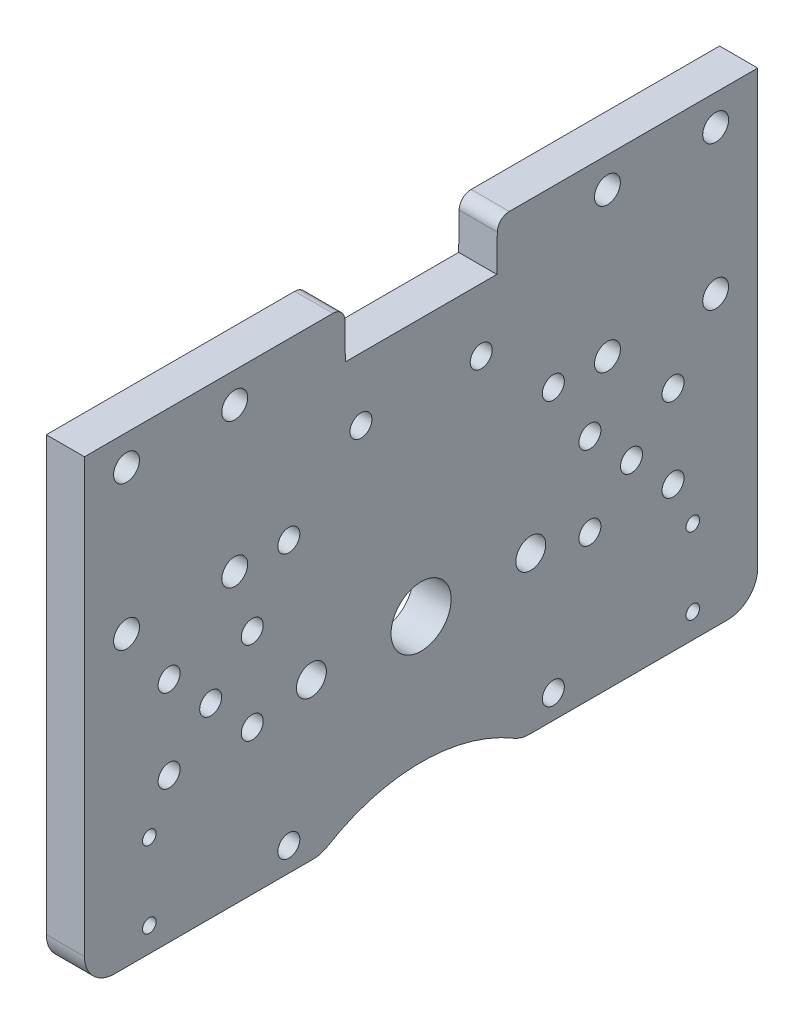
SolidWorks part; units mm, degrees
ref_plane "Front Plane" through (0, 0, 0) normal (0, 0, 1) x (1, 0, 0)
ref_plane "Top Plane" through (0, 0, 0) normal (0, 1, 0) x (1, 0, 0)
ref_plane "Right Plane" through (0, 0, 0) normal (1, 0, 0) x (0, 0, -1)
sketch "Sketch1" plane through (0, 0, 0) normal (1, 0, 0) x (0, 0, -1)
  line L1 (-56, -26) -> (56, -26)
  line L2 (-56, -26) -> (-56, 51)
  line L3 (-56, 51) -> (56, 51)
  line L4 (56, -26) -> (56, 51)
  point P0 (0, 0)
  point P6 (0, -26)
  dimension "D1" = 77
  dimension "D2" = 112
  dimension "D3" = 26
extrude "Boss-Extrude1" add sketch "Sketch1" along normal blind 6.35
sketch "Sketch2" plane through (6.35, 0, 0) normal (1, 0, 0) x (0, 0, -1)
  line L1 (-22, -22) -> (22, -22) construction
  line L2 (-22, -22) -> (-22, 22) construction
  line L3 (-22, 22) -> (22, 22) construction
  line L4 (22, -22) -> (22, 22) construction
  line L5 (-22, -22) -> (22, 22) construction
  line L6 (-22, 22) -> (22, -22) construction
  point P0 (0, 0)
  dimension "D1" = 44
  dimension "D2" = 44
hole_wizard "#6 Clearance Hole1" positions "Sketch4" profile "Sketch3" hole size "#6" standard "ANSI Inch" end condition through all
sketch "Sketch4" plane through (6.35, 0, 0) normal (1, 0, 0) x (0, 0, -1)
  point P0 (-22, 22)
  point P3 (22, 22)
  point P6 (22, -22)
  point P9 (-22, -22)
sketch "Sketch3" plane through (6.35, 22, 22) normal (0, 1, 0) x (0, 0, -1)
  line L0 (0, 0) -> (0, 6.35)
  line L1 (0, 6.35) -> (1.8288, 6.35)
  line L2 (1.8288, 6.35) -> (1.8288, 0)
  line L5 (1.8288, 0) -> (0, 0)
  line L11 (0, -6.35) -> (0, 107.95) construction
  dimension "Thru Hole Dia." = 3.6576
  dimension "Thru Hole Depth" = 6.35
sketch "Sketch5" plane through (6.35, 0, 0) normal (1, 0, 0) x (0, 0, -1)
  circle A0 centre (0, 0) radius 5
  dimension "D1" = 10
extrude "Cut-Extrude1" cut sketch "Sketch5" against normal through all
sketch "Sketch7" plane through (6.35, 0, 0) normal (1, 0, 0) x (0, 0, -1)
  line L0 (-41.9148, -1.9148) -> (-41.9148, 11.9148) construction
  line L1 (-41.9148, -1.9148) -> (-28.0852, -1.9148) construction
  line L2 (-41.9148, 11.9148) -> (-28.0852, 11.9148) construction
  line L3 (-28.0852, -1.9148) -> (-28.0852, 11.9148) construction
  line L4 (-41.9148, -1.9148) -> (-28.0852, 11.9148) construction
  line L5 (-41.9148, 11.9148) -> (-28.0852, -1.9148) construction
  line L6 (41.9148, -1.9148) -> (41.9148, 11.9148) construction
  line L7 (41.9148, -1.9148) -> (28.0852, -1.9148) construction
  line L8 (41.9148, 11.9148) -> (28.0852, 11.9148) construction
  line L9 (28.0852, -1.9148) -> (28.0852, 11.9148) construction
  line L10 (41.9148, -1.9148) -> (28.0852, 11.9148) construction
  line L11 (41.9148, 11.9148) -> (28.0852, -1.9148) construction
  line L12 (-35, 5) -> (35, 5) construction
  point P1 (-35, 5)
  point P2 (35, 5)
  point P8 (0, 5)
  dimension "D1" = 19.558
  dimension "D2" = 19.558
  dimension "D3" = 70
  dimension "D4" = 5
hole_wizard "#6 Clearance Hole2" positions "Sketch9" profile "Sketch8" hole size "#6" standard "ANSI Inch" end condition through all
sketch "Sketch9" plane through (6.35, 0, 0) normal (1, 0, 0) x (0, 0, -1)
  point P0 (-41.9148, 11.9148)
  point P3 (-28.0852, 11.9148)
  point P6 (-28.0852, -1.9148)
  point P9 (-41.9148, -1.9148)
  point P12 (28.0852, 11.9148)
  point P15 (28.0852, -1.9148)
  point P18 (41.9148, -1.9148)
  point P21 (41.9148, 11.9148)
  point P24 (-35, 5)
  point P27 (35, 5)
sketch "Sketch8" plane through (6.35, 11.9148, 41.9148) normal (0, 1, 0) x (0, 0, -1)
  line L0 (0, 0) -> (0, 6.35)
  line L1 (0, 6.35) -> (1.8288, 6.35)
  line L2 (1.8288, 6.35) -> (1.8288, 0)
  line L5 (1.8288, 0) -> (0, 0)
  line L11 (0, -6.35) -> (0, 107.95) construction
  dimension "Thru Hole Dia." = 3.6576
  dimension "Thru Hole Depth" = 6.35
sketch "Sketch11" plane through (0, 0, 0) normal (-1, 0, 0) x (0, 0, 1)
  line L0 (-18.25, 0) -> (18.25, 0) construction
  point P4 (0, 0)
  dimension "D1" = 36.5
hole_wizard "#10 Clearance Hole1" positions "Sketch13" profile "Sketch12" hole size "#10" standard "ANSI Inch" end condition through all
sketch "Sketch13" plane through (0, 0, 0) normal (-1, 0, 0) x (0, 0, 1)
  point P0 (18.25, 0)
  point P3 (-18.25, 0)
sketch "Sketch12" plane through (0, 0, 18.25) normal (0, 1, 0) x (0, 0, 1)
  line L0 (0, 0) -> (0, 6.35)
  line L1 (0, 6.35) -> (2.4892, 6.35)
  line L2 (2.4892, 6.35) -> (2.4892, 0)
  line L5 (2.4892, 0) -> (0, 0)
  line L11 (0, -6.35) -> (0, 107.95) construction
  dimension "Thru Hole Dia." = 4.9784
  dimension "Thru Hole Depth" = 6.35
sketch "Sketch20" plane through (0, 0, 0) normal (-1, 0, 0) x (0, 0, 1)
  line L0 (56, 51) -> (56, -26) construction
  line L1 (49, 45.97) -> (31, 45.97) construction
  line L2 (49, 45.97) -> (49, 21.97) construction
  line L3 (49, 21.97) -> (31, 21.97) construction
  line L4 (31, 45.97) -> (31, 21.97) construction
  line L5 (-31, 45.97) -> (-49, 45.97) construction
  line L6 (-31, 45.97) -> (-31, 21.97) construction
  line L7 (-31, 21.97) -> (-49, 21.97) construction
  line L8 (-49, 45.97) -> (-49, 21.97) construction
  line L9 (-56, -26) -> (-56, 51) construction
  line L10 (-56, 51) -> (56, 51) construction
  dimension "D1" = 18
  dimension "D2" = 24
  dimension "D3" = 7
  dimension "D4" = 7
  dimension "D5" = 5.03
hole_wizard "#8 Clearance Hole2" positions "3DSketch3" profile "Sketch21" hole size "#8" standard "ANSI Inch" end condition through all
sketch3d "3DSketch3"
  point P0 (0, 45.97, 49)
  point P3 (0, 45.97, 31)
  point P6 (0, 21.97, 31)
  point P9 (0, 21.97, 49)
  point P12 (0, 45.97, -31)
  point P15 (0, 21.97, -31)
  point P18 (0, 21.97, -49)
  point P21 (0, 45.97, -49)
sketch "Sketch21" plane through (0, 45.97, 49) normal (0, 1, 0) x (0, 0, 1)
  line L0 (0, 0) -> (0, 6.35)
  line L1 (0, 6.35) -> (2.1526, 6.35)
  line L2 (2.1526, 6.35) -> (2.1526, 0)
  line L5 (2.1526, 0) -> (0, 0)
  line L11 (0, -6.35) -> (0, 107.95) construction
  dimension "Thru Hole Dia." = 4.3053
  dimension "Thru Hole Depth" = 6.35
sketch "Sketch22" plane through (0, 0, 0) normal (-1, 0, 0) x (0, 0, 1)
  line L0 (12.7, 51) -> (-12.7, 51)
  line L1 (-56, 51) -> (56, 51) construction
  line L2 (-12.7, 51) -> (-12.6, 42.97)
  line L3 (-12.6, 42.97) -> (12.6, 42.97)
  line L4 (12.6, 42.97) -> (12.7, 51)
  point P4 (0, 42.97)
  point P7 (0, 51)
  dimension "D1" = 25.4
  dimension "D2" = 25.2
  dimension "D3" = 8.03
extrude "Cut-Extrude2" cut sketch "Sketch22" against normal through all
sketch "Sketch23" plane through (0, 0, 0) normal (-1, 0, 0) x (0, 0, 1)
  line L0 (10, 32.5052) -> (-10, 32.5052) construction
  line L1 (-12.6, 42.97) -> (12.6, 42.97) construction
  point P2 (0, 32.5052)
  dimension "D1" = 10.4648
  dimension "D2" = 20
hole_wizard "#6 Clearance Hole3" positions "3DSketch4" profile "Sketch24" hole size "#6" standard "ANSI Inch" end condition through all
sketch3d "3DSketch4"
  point P0 (0, 32.5052, 10)
  point P3 (0, 32.5052, -10)
sketch "Sketch24" plane through (0, 32.5052, 10) normal (0, 1, 0) x (0, 0, 1)
  line L0 (0, 0) -> (0, 6.35)
  line L1 (0, 6.35) -> (1.8288, 6.35)
  line L2 (1.8288, 6.35) -> (1.8288, 0)
  line L5 (1.8288, 0) -> (0, 0)
  line L11 (0, -6.35) -> (0, 107.95) construction
  dimension "Thru Hole Dia." = 3.6576
  dimension "Thru Hole Depth" = 6.35
fillet "Fillet2" radius 2 2 edges at (3.175, 51, -12.7) (3.175, 51, 12.7)
sketch "Sketch25" plane through (0, 0, 0) normal (-1, 0, 0) x (0, 0, 1)
  line L0 (56, -26) -> (-56, -26) construction
  circle A0 centre (0, -51) radius 30
  point P6 (0, -26)
  dimension "D1" = 60
  dimension "D2" = 25
extrude "Cut-Extrude3" cut sketch "Sketch25" against normal through all
fillet "Fillet1" radius 5 4 edges at (3.175, -26, -56) (3.175, -26, 56) (3.175, -26, 16.5831) (3.175, -26, -16.5831)
sketch "Sketch26" plane through (0, 0, 0) normal (-1, 0, 0) x (0, 0, 1)
  line L0 (45.205, -9.224) -> (45.205, -21.924) construction
  line L1 (56, 51) -> (56, -21) construction
  circle A1 centre (35, 5) radius 1.8288 construction
  point P2 (45.205, -15.574)
  dimension "D1" = 12.7
  dimension "D2" = 20.574
  dimension "D3" = 10.795
hole_wizard "Tap Drill for #4-40 Tap1" positions "3DSketch5" profile "Sketch27" hole size "#4-40" standard "ANSI Inch" end condition through all
sketch3d "3DSketch5"
  point P0 (0, -21.924, 45.205)
  point P3 (0, -9.224, 45.205)
sketch "Sketch27" plane through (0, -21.924, 45.205) normal (0, 1, 0) x (0, 0, 1)
  line L0 (0, 0) -> (0, 6.35)
  line L1 (0, 6.35) -> (1.1303, 6.35)
  line L2 (1.1303, 6.35) -> (1.1303, 0)
  line L5 (1.1303, 0) -> (0, 0)
  line L11 (0, -6.35) -> (0, 107.95) construction
  dimension "Thru Hole Dia." = 2.2606
  dimension "Thru Hole Depth" = 6.35
mirror "Mirror1" about plane through (0, 0, 0) normal (0, 0, 1) of "Tap Drill for #4-40 Tap1"
